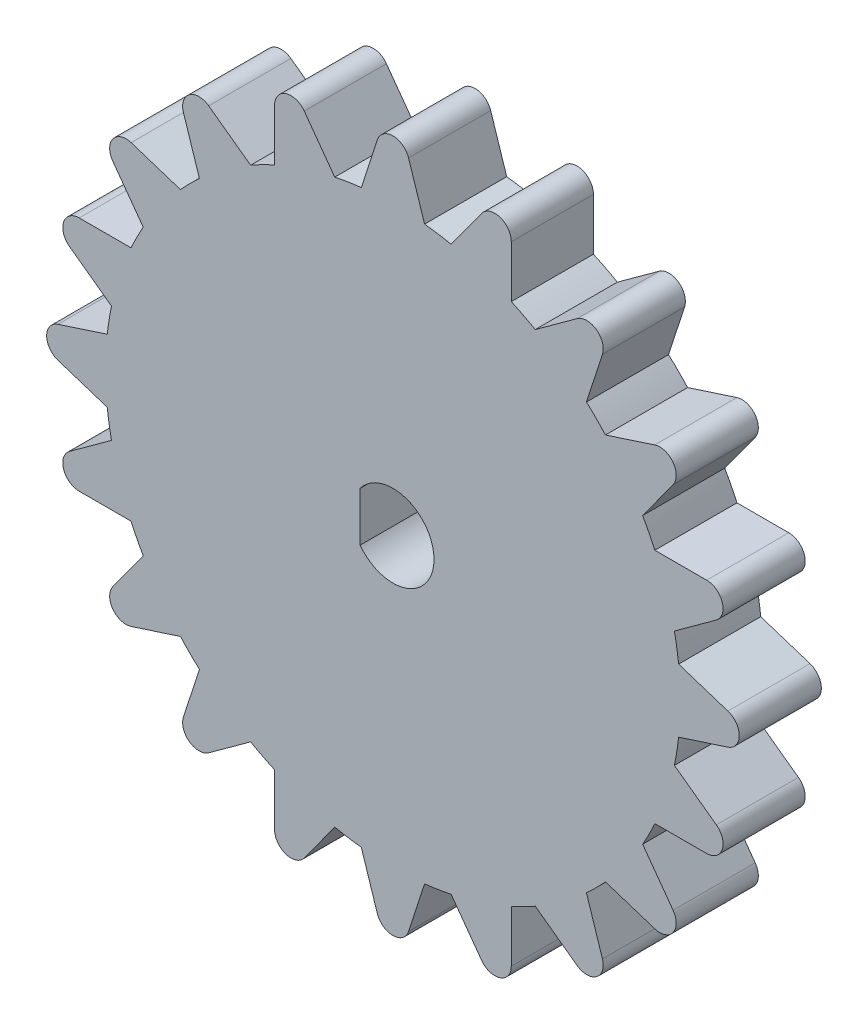
SolidWorks part; units mm, degrees
ref_plane "Płaszczyzna przednia" through (0, 0, 0) normal (0, 0, 1) x (1, 0, 0)
ref_plane "Płaszczyzna górna" through (0, 0, 0) normal (0, 1, 0) x (1, 0, 0)
ref_plane "Płaszczyzna prawa" through (0, 0, 0) normal (1, 0, 0) x (0, 0, -1)
sketch "Szkic1" plane through (0, 0, 0) normal (0, 0, 1) x (1, 0, 0)
  line L0 (-2, 1.5) -> (-2, -1.5)
  line L1 (-0.951, 20.3937) -> (-1.9259, 17.3937)
  line L2 (0, 27.2612) -> (0, -6.5612) construction
  line L3 (0.951, 20.3937) -> (1.9259, 17.3937)
  line L4 (7.2065, 19.1017) -> (7.2066, 15.9472)
  line L5 (5.3975, 19.6895) -> (3.5433, 17.1375)
  line L6 (12.7565, 15.9398) -> (11.7819, 12.9398)
  line L7 (11.2177, 17.0579) -> (8.6657, 15.2038)
  line L8 (17.0579, 11.2177) -> (15.2038, 8.6657)
  line L9 (15.9398, 12.7565) -> (12.9398, 11.7819)
  line L10 (19.6895, 5.3975) -> (17.1375, 3.5433)
  line L11 (19.1017, 7.2065) -> (15.9472, 7.2066)
  line L12 (20.3937, -0.951) -> (17.3937, -1.9259)
  line L13 (20.3937, 0.951) -> (17.3937, 1.9259)
  line L14 (19.1017, -7.2065) -> (15.9472, -7.2066)
  line L15 (19.6895, -5.3975) -> (17.1375, -3.5433)
  line L16 (15.9398, -12.7565) -> (12.9398, -11.7819)
  line L17 (17.0579, -11.2177) -> (15.2038, -8.6657)
  line L18 (11.2177, -17.0579) -> (8.6657, -15.2038)
  line L19 (12.7565, -15.9398) -> (11.7819, -12.9398)
  line L20 (5.3975, -19.6895) -> (3.5433, -17.1375)
  line L21 (7.2065, -19.1017) -> (7.2066, -15.9472)
  line L22 (-0.951, -20.3937) -> (-1.9259, -17.3937)
  line L23 (0.951, -20.3937) -> (1.9259, -17.3937)
  line L24 (-7.2065, -19.1017) -> (-7.2066, -15.9472)
  line L25 (-5.3975, -19.6895) -> (-3.5433, -17.1375)
  line L26 (-12.7565, -15.9398) -> (-11.7819, -12.9398)
  line L27 (-11.2177, -17.0579) -> (-8.6657, -15.2038)
  line L28 (-17.0579, -11.2177) -> (-15.2038, -8.6657)
  line L29 (-15.9398, -12.7565) -> (-12.9398, -11.7819)
  line L30 (-19.6895, -5.3975) -> (-17.1375, -3.5433)
  line L31 (-19.1017, -7.2065) -> (-15.9472, -7.2066)
  line L32 (-20.3937, 0.951) -> (-17.3937, 1.9259)
  line L33 (-20.3937, -0.951) -> (-17.3937, -1.9259)
  line L34 (-19.1017, 7.2065) -> (-15.9472, 7.2066)
  line L35 (-19.6895, 5.3975) -> (-17.1375, 3.5433)
  line L36 (-15.9398, 12.7565) -> (-12.9398, 11.7819)
  line L37 (-17.0579, 11.2177) -> (-15.2038, 8.6657)
  line L38 (-11.2177, 17.0579) -> (-8.6657, 15.2038)
  line L39 (-12.7565, 15.9398) -> (-11.7819, 12.9398)
  line L40 (-5.3975, 19.6895) -> (-3.5433, 17.1375)
  line L41 (-7.2065, 19.1017) -> (-7.2066, 15.9472)
  arc A0 (-2, -1.5) -> (-2, 1.5) centre (0, 0) ccw
  arc A1 (-1.9259, 17.3937) -> (-3.5433, 17.1375) centre (0, 0) ccw
  arc A2 (0.951, 20.3937) -> (-0.951, 20.3937) centre (0, 20.0846) ccw
  arc A3 (7.2065, 19.1017) -> (5.3975, 19.6895) centre (6.2065, 19.1016) ccw
  arc A4 (12.7565, 15.9398) -> (11.2177, 17.0579) centre (11.8055, 16.2488) ccw
  arc A5 (17.0579, 11.2177) -> (15.9398, 12.7565) centre (16.2488, 11.8055) ccw
  arc A6 (19.6895, 5.3975) -> (19.1017, 7.2065) centre (19.1016, 6.2065) ccw
  arc A7 (20.3937, -0.951) -> (20.3937, 0.951) centre (20.0846, 0) ccw
  arc A8 (19.1017, -7.2065) -> (19.6895, -5.3975) centre (19.1016, -6.2065) ccw
  arc A9 (15.9398, -12.7565) -> (17.0579, -11.2177) centre (16.2488, -11.8055) ccw
  arc A10 (11.2177, -17.0579) -> (12.7565, -15.9398) centre (11.8055, -16.2488) ccw
  arc A11 (5.3975, -19.6895) -> (7.2065, -19.1017) centre (6.2065, -19.1016) ccw
  arc A12 (-0.951, -20.3937) -> (0.951, -20.3937) centre (0, -20.0846) ccw
  arc A13 (-7.2065, -19.1017) -> (-5.3975, -19.6895) centre (-6.2065, -19.1016) ccw
  arc A14 (-12.7565, -15.9398) -> (-11.2177, -17.0579) centre (-11.8055, -16.2488) ccw
  arc A15 (-17.0579, -11.2177) -> (-15.9398, -12.7565) centre (-16.2488, -11.8055) ccw
  arc A16 (-19.6895, -5.3975) -> (-19.1017, -7.2065) centre (-19.1016, -6.2065) ccw
  arc A17 (-20.3937, 0.951) -> (-20.3937, -0.951) centre (-20.0846, 0) ccw
  arc A18 (-19.1017, 7.2065) -> (-19.6895, 5.3975) centre (-19.1016, 6.2065) ccw
  arc A19 (-15.9398, 12.7565) -> (-17.0579, 11.2177) centre (-16.2488, 11.8055) ccw
  arc A20 (-11.2177, 17.0579) -> (-12.7565, 15.9398) centre (-11.8055, 16.2488) ccw
  arc A21 (-5.3975, 19.6895) -> (-7.2065, 19.1017) centre (-6.2065, 19.1016) ccw
  arc A22 (3.5433, 17.1375) -> (1.9259, 17.3937) centre (0, 0) ccw
  arc A23 (8.6657, 15.2038) -> (7.2066, 15.9472) centre (0, 0) ccw
  arc A24 (12.9398, 11.7819) -> (11.7819, 12.9398) centre (0, 0) ccw
  arc A25 (15.9472, 7.2066) -> (15.2038, 8.6657) centre (0, 0) ccw
  arc A26 (17.3937, 1.9259) -> (17.1375, 3.5433) centre (0, 0) ccw
  arc A27 (17.1375, -3.5433) -> (17.3937, -1.9259) centre (0, 0) ccw
  arc A28 (15.2038, -8.6657) -> (15.9472, -7.2066) centre (0, 0) ccw
  arc A29 (11.7819, -12.9398) -> (12.9398, -11.7819) centre (0, 0) ccw
  arc A30 (7.2066, -15.9472) -> (8.6657, -15.2038) centre (0, 0) ccw
  arc A31 (1.9259, -17.3937) -> (3.5433, -17.1375) centre (0, 0) ccw
  arc A32 (-3.5433, -17.1375) -> (-1.9259, -17.3937) centre (0, 0) ccw
  arc A33 (-8.6657, -15.2038) -> (-7.2066, -15.9472) centre (0, 0) ccw
  arc A34 (-12.9398, -11.7819) -> (-11.7819, -12.9398) centre (0, 0) ccw
  arc A35 (-17.3937, -1.9259) -> (-17.1375, -3.5433) centre (0, 0) ccw
  arc A36 (-17.1375, 3.5433) -> (-17.3937, 1.9259) centre (0, 0) ccw
  arc A37 (-15.9472, -7.2066) -> (-15.2038, -8.6657) centre (0, 0) ccw
  arc A38 (-15.2038, 8.6657) -> (-15.9472, 7.2066) centre (0, 0) ccw
  arc A39 (-11.7819, 12.9398) -> (-12.9398, 11.7819) centre (0, 0) ccw
  arc A40 (-7.2066, 15.9472) -> (-8.6657, 15.2038) centre (0, 0) ccw
  point P12 (0, 23.3204)
  point P110 (0, 0)
  dimension "D1" = 5
  dimension "D3" = 1
  dimension "D4" = 35
  dimension "D2" = 2
  dimension "D5" = 18.002
  dimension "D6" = 3
  dimension "D7" = 20
extrude "Dodanie-wyciągnięcie1" add sketch "Szkic1" along normal blind 5
